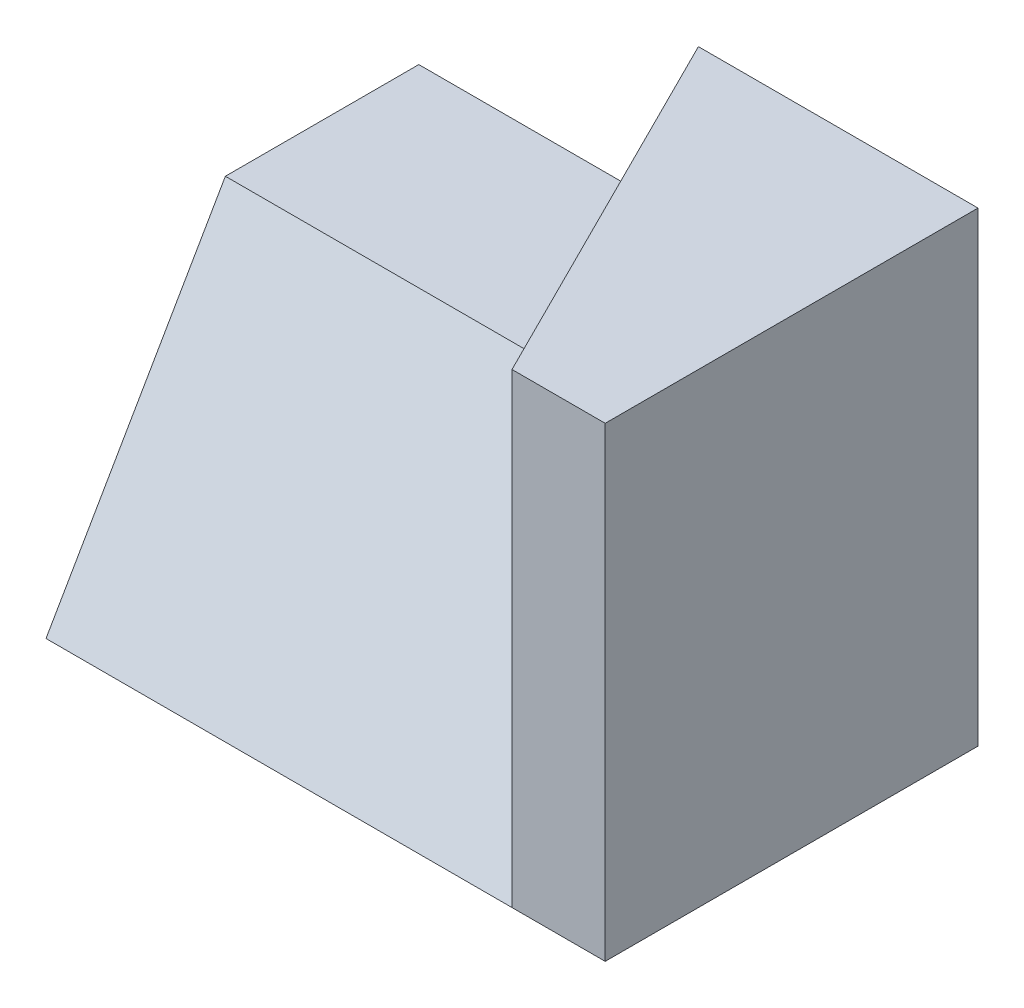
SolidWorks part; units mm, degrees
ref_plane "Front Plane" through (0, 0, 0) normal (0, 0, 1) x (1, 0, 0)
ref_plane "Top Plane" through (0, 0, 0) normal (0, 1, 0) x (1, 0, 0)
ref_plane "Right Plane" through (0, 0, 0) normal (1, 0, 0) x (0, 0, -1)
sketch "Sketch1" plane through (0, 0, 0) normal (0, 1, 0) x (1, 0, 0)
  line L1 (0, 0) -> (90, 0)
  line L2 (0, 0) -> (0, 60)
  line L3 (0, 60) -> (90, 60)
  line L4 (90, 0) -> (90, 60)
  dimension "D1" = 90
  dimension "D2" = 60
extrude "Extrude1" add sketch "Sketch1" along normal blind 50
sketch "Sketch2" plane through (90, 0, 0) normal (1, 0, 0) x (0, 0, -1)
  line L0 (0, 0) -> (28.8675, 50)
  line L1 (0, 50) -> (60, 50) construction
  line L2 (28.8675, 50) -> (0, 50)
  line L3 (0, 50) -> (0, 0)
  line L4 (0, 0) -> (60, 0) construction
  dimension "D1" = 60
extrude "Extrude2" cut sketch "Sketch2" against normal through all
sketch "Sketch3" plane through (0, 0, 0) normal (0, 1, 0) x (1, 0, 0)
  line L0 (90, 60) -> (90, 0)
  line L1 (90, 0) -> (75, 0)
  line L2 (0, 0) -> (90, 0) construction
  line L3 (75, 0) -> (45, 60)
  line L4 (90, 60) -> (0, 60) construction
  line L5 (45, 60) -> (90, 60)
  dimension "D1" = 45
  dimension "D2" = 15
extrude "Extrude3" add sketch "Sketch3" along normal blind 75
